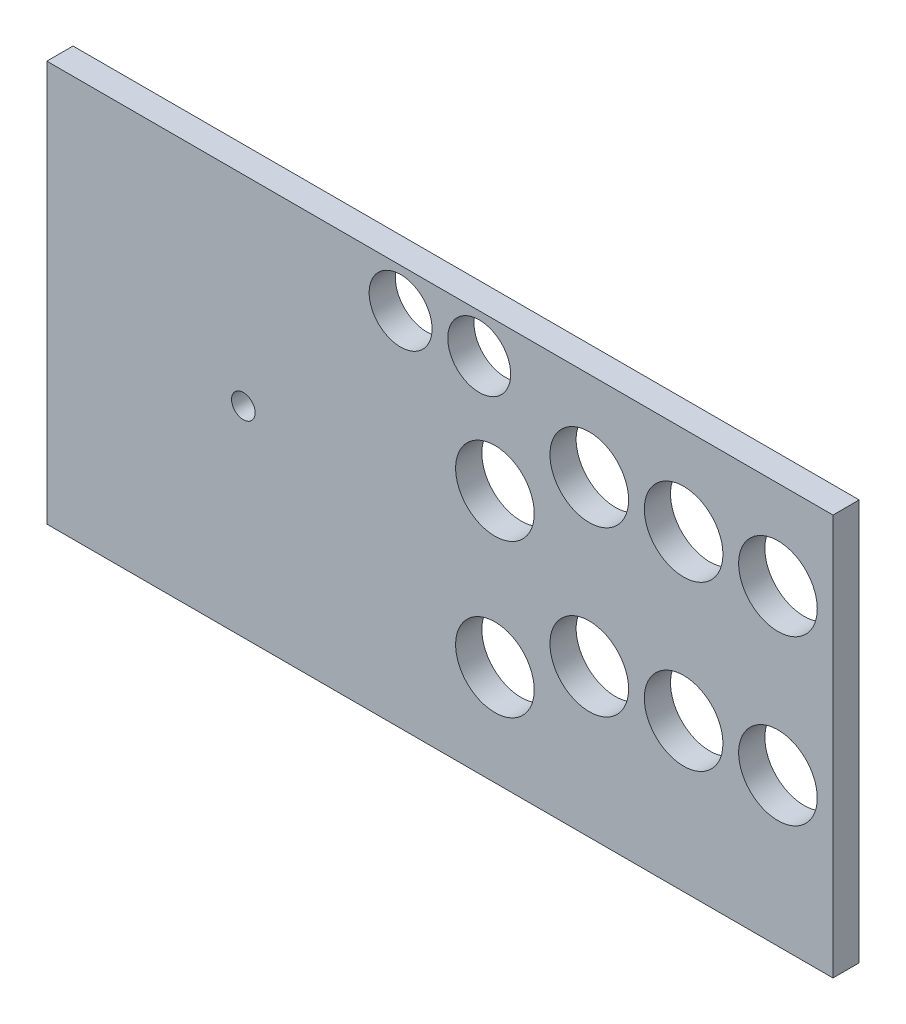
SolidWorks part; units mm, degrees
ref_plane "Plan de face" through (0, 0, 0) normal (0, 0, 1) x (1, 0, 0)
ref_plane "Plan de dessus" through (0, 0, 0) normal (0, 1, 0) x (1, 0, 0)
ref_plane "Plan de droite" through (0, 0, 0) normal (1, 0, 0) x (0, 0, -1)
sketch "Esquisse1" plane through (0, 0, 0) normal (0, 0, 1) x (1, 0, 0)
  line L0 (0, 76.5) -> (300, 76.5) construction
  line L1 (0, 0) -> (300, 0)
  line L2 (0, 0) -> (0, 153)
  line L3 (0, 153) -> (300, 153)
  line L4 (300, 0) -> (300, 153)
  line L5 (150, 153) -> (150, 0) construction
  dimension "D1" = 300
  dimension "D2" = 153
extrude "Boss.-Extru.1" add sketch "Esquisse1" along normal blind 10
sketch "Esquisse2" plane through (0, 0, 10) normal (0, 0, 1) x (1, 0, 0)
  line L0 (150, 153) -> (150, 0) construction
  line L1 (300, 153) -> (0, 153) construction
  line L2 (0, 0) -> (300, 0) construction
  line L3 (150, 0) -> (150, 76.5) construction
  line L4 (150, 76.5) -> (300, 76.5) construction
  line L5 (300, 0) -> (300, 153) construction
  line L6 (0, 153) -> (0, 0) construction
  line L7 (45, 124) -> (105, 124)
  line L8 (45, 124) -> (45, 29)
  line L9 (45, 29) -> (105, 29)
  line L10 (105, 124) -> (105, 29)
  line L11 (75, 124) -> (75, 29) construction
  line L12 (45, 76.5) -> (105, 76.5) construction
  circle A0 centre (75, 76.5) radius 4.5
  dimension "D5" = 9
  dimension "D1" = 60
  dimension "D2" = 95
  dimension "D3" = 29
  dimension "D4" = 45
sketch "Esquisse7" plane through (0, 0, 10) normal (0, 0, 1) x (1, 0, 0)
  line L0 (150, 76.5) -> (300, 76.5) construction
  line L1 (150, 153) -> (150, 0) construction
  circle A0 centre (171, 96.5) radius 15
  dimension "D1" = 30
  dimension "D2" = 20
  dimension "D3" = 21
extrude "Enlèv. mat.-Extru.5" cut sketch "Esquisse7" against normal through all contours A0
sketch "Esquisse8" plane through (0, 0, 10) normal (0, 0, 1) x (1, 0, 0)
  line L0 (150, 76.5) -> (300, 76.5) construction
  circle A0 centre (207, 119) radius 15
  circle A1 centre (171, 96.5) radius 15 construction
  dimension "D1" = 30
  dimension "D2" = 36
  dimension "D3" = 42.5
extrude "Enlèv. mat.-Extru.6" cut sketch "Esquisse8" against normal through all
sketch "Esquisse9" plane through (0, 0, 10) normal (0, 0, 1) x (1, 0, 0)
  line L0 (150, 76.5) -> (300, 76.5) construction
  circle A0 centre (243, 119) radius 15
  circle A1 centre (207, 119) radius 15 construction
  dimension "D1" = 30
  dimension "D2" = 36
  dimension "D3" = 42.5
extrude "Enlèv. mat.-Extru.7" cut sketch "Esquisse9" against normal through all
sketch "Esquisse10" plane through (0, 0, 10) normal (0, 0, 1) x (1, 0, 0)
  line L0 (150, 76.5) -> (300, 76.5) construction
  circle A0 centre (279, 119) radius 15
  circle A1 centre (243, 119) radius 15 construction
  dimension "D1" = 30
  dimension "D2" = 36
  dimension "D3" = 42.5
extrude "Enlèv. mat.-Extru.8" cut sketch "Esquisse10" against normal through all
sketch "Esquisse11" plane through (0, 0, 10) normal (0, 0, 1) x (1, 0, 0)
  line L0 (150, 76.5) -> (300, 76.5) construction
  line L1 (150, 153) -> (150, 0) construction
  circle A0 centre (171, 38.2) radius 15
  dimension "D1" = 30
  dimension "D2" = 38.3
  dimension "D3" = 21
extrude "Enlèv. mat.-Extru.9" cut sketch "Esquisse11" against normal through all
sketch "Esquisse12" plane through (0, 0, 10) normal (0, 0, 1) x (1, 0, 0)
  line L0 (150, 76.5) -> (300, 76.5) construction
  circle A0 centre (207, 56.5) radius 15
  circle A1 centre (171, 38.2) radius 15 construction
  dimension "D1" = 30
  dimension "D2" = 20
  dimension "D3" = 36
extrude "Enlèv. mat.-Extru.10" cut sketch "Esquisse12" against normal through all
sketch "Esquisse13" plane through (0, 0, 10) normal (0, 0, 1) x (1, 0, 0)
  line L0 (150, 76.5) -> (300, 76.5) construction
  circle A0 centre (243, 56.5) radius 15
  circle A1 centre (207, 56.5) radius 15 construction
  dimension "D1" = 30
  dimension "D2" = 20
  dimension "D3" = 36
extrude "Enlèv. mat.-Extru.11" cut sketch "Esquisse13" against normal through all
sketch "Esquisse14" plane through (0, 0, 10) normal (0, 0, 1) x (1, 0, 0)
  line L0 (150, 76.5) -> (300, 76.5) construction
  circle A0 centre (279, 56.5) radius 15
  circle A1 centre (243, 56.5) radius 15 construction
  dimension "D1" = 30
  dimension "D2" = 20
  dimension "D3" = 36
extrude "Enlèv. mat.-Extru.12" cut sketch "Esquisse14" against normal through all
sketch "Esquisse16" plane through (0, 0, 10) normal (0, 0, 1) x (1, 0, 0)
  line L0 (300, 153) -> (0, 153) construction
  line L1 (150, 153) -> (150, 0) construction
  circle A0 centre (165, 138) radius 12
  dimension "D3" = 24
  dimension "D1" = 15
  dimension "D2" = 15
extrude "Enlèv. mat.-Extru.14" cut sketch "Esquisse16" against normal through all
sketch "Esquisse17" plane through (0, 0, 10) normal (0, 0, 1) x (1, 0, 0)
  line L0 (150, 153) -> (150, 0) construction
  line L1 (300, 153) -> (0, 153) construction
  circle A0 centre (135, 138) radius 12
  dimension "D3" = 24
  dimension "D1" = 15
  dimension "D2" = 15
extrude "Enlèv. mat.-Extru.15" cut sketch "Esquisse17" against normal through all contours A0
extrude "Enlèv. mat.-Extru.16" cut sketch "Esquisse2" against normal through all contours A0
